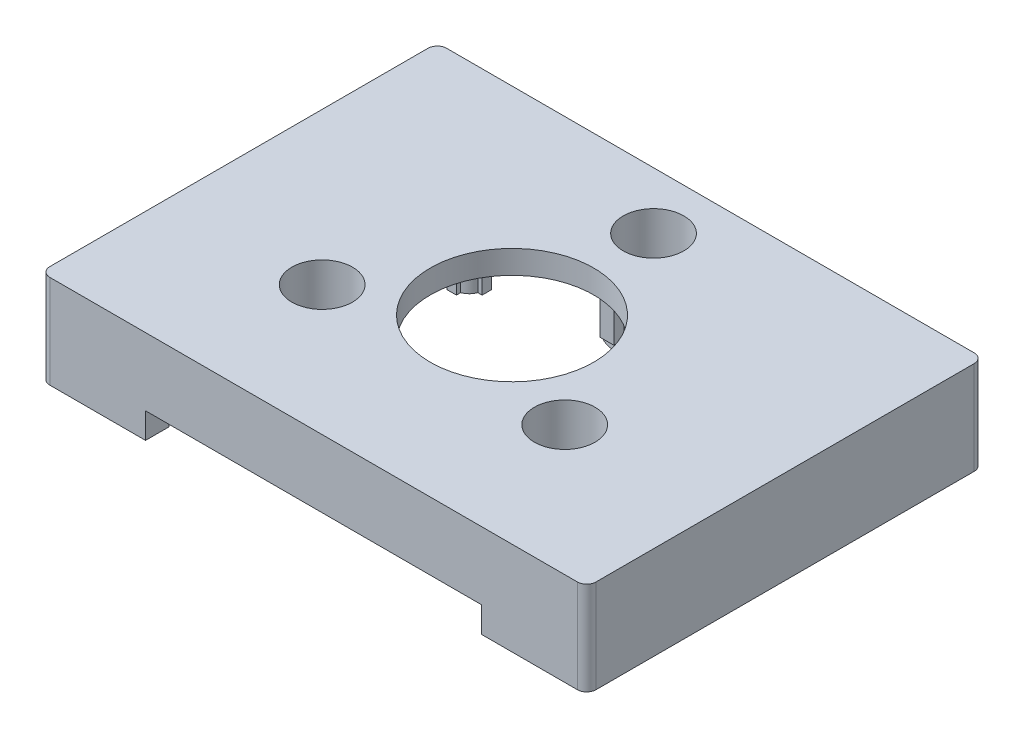
SolidWorks part; units mm, degrees
ref_plane "Front Plane" through (0, 0, 0) normal (0, 0, 1) x (1, 0, 0)
ref_plane "Top Plane" through (0, 0, 0) normal (0, 1, 0) x (1, 0, 0)
ref_plane "Right Plane" through (0, 0, 0) normal (1, 0, 0) x (0, 0, -1)
sketch "Sketch1" plane through (0, 0, 0) normal (0, 1, 0) x (1, 0, 0)
  line L1 (-58.5, 42.5) -> (58.5, 42.5)
  line L2 (-58.5, 42.5) -> (-58.5, -42.5)
  line L3 (-58.5, -42.5) -> (58.5, -42.5)
  line L4 (58.5, 42.5) -> (58.5, -42.5)
  dimension "D1" = 85
  dimension "D2" = 117
  dimension "D3" = 58.5
  dimension "D4" = 42.5
extrude "Boss-Extrude1" add sketch "Sketch1" along normal blind 20
sketch "Sketch2" plane through (0, 0, 0) normal (0, -1, 0) x (-1, 0, 0)
  line L0 (58.5, 42.5) -> (58.5, -42.5) construction
  line L1 (53.5, -37.5) -> (-53.5, -37.5)
  line L2 (53.5, -37.5) -> (53.5, 37.5)
  line L3 (53.5, 37.5) -> (-53.5, 37.5)
  line L4 (-53.5, -37.5) -> (-53.5, 37.5)
  line L5 (58.5, -42.5) -> (-58.5, -42.5) construction
  line L6 (-58.5, -42.5) -> (-58.5, 42.5) construction
  line L7 (-58.5, 42.5) -> (58.5, 42.5) construction
  dimension "D1" = 5
  dimension "D2" = 5
  dimension "D3" = 5
  dimension "D4" = 5
extrude "Cut-Extrude1" cut sketch "Sketch2" against normal blind 15
fillet "Fillet1" radius 2 1 edges at (-58.5, 10, 42.5)
fillet "Fillet2" radius 2 1 edges at (58.5, 10, 42.5)
fillet "Fillet3" radius 2 1 edges at (58.5, 10, -42.5)
fillet "Fillet4" radius 2 1 edges at (-58.5, 10, -42.5)
sketch "Sketch3" plane through (0, 0, 0) normal (0, -1, 0) x (1, 0, 0)
  line L0 (-56.5, 42.5) -> (56.5, 42.5) construction
  line L1 (-58.5, -40.5) -> (-58.5, 40.5) construction
  line L2 (58.5, 40.5) -> (58.5, -40.5) construction
  line L3 (56.5, -42.5) -> (-56.5, -42.5) construction
  circle A0 centre (-54.8, 38.8) radius 3.5
  circle A1 centre (54.8, 38.8) radius 3.5
  circle A2 centre (54.8, -38.8) radius 3.5
  circle A3 centre (-54.8, -38.8) radius 3.5
  dimension "D2" = 7
  dimension "D4" = 7
  dimension "D7" = 7
  dimension "D12" = 7
  dimension "D1" = 3.7
  dimension "D3" = 3.7
  dimension "D5" = 3.7
  dimension "D6" = 3.7
  dimension "D8" = 3.7
  dimension "D9" = 3.7
  dimension "D10" = 3.7
  dimension "D11" = 3.7
extrude "Boss-Extrude2" add sketch "Sketch3" against normal blind 16
sketch "Sketch4" plane through (0, 0, 0) normal (0, -1, 0) x (1, 0, 0)
  line L0 (56.5, -42.5) -> (-56.5, -42.5) construction
  line L1 (-58.5, -40.5) -> (-58.5, 40.5) construction
  line L2 (58.5, 40.5) -> (58.5, -40.5) construction
  line L3 (-56.5, 42.5) -> (56.5, 42.5) construction
  circle A0 centre (-54.8, 38.8) radius 1.5
  circle A1 centre (54.8, 38.8) radius 1.5
  circle A2 centre (54.8, -38.8) radius 1.5
  circle A3 centre (-54.8, -38.8) radius 1.5
  dimension "D1" = 3
  dimension "D4" = 3
  dimension "D5" = 3
  dimension "D8" = 3
  dimension "D2" = 3.7
  dimension "D3" = 3.7
  dimension "D6" = 3.7
  dimension "D7" = 3.7
  dimension "D9" = 3.7
  dimension "D10" = 3.7
extrude "Cut-Extrude2" cut sketch "Sketch4" against normal blind 15
sketch "Sketch5" plane through (0, 0, 42.5) normal (0, 0, 1) x (1, 0, 0)
  line L0 (-56.5, 0) -> (56.5, 0) construction
  line L1 (-36, 0) -> (36, 0)
  line L2 (-36, 0) -> (-36, 5.5)
  line L3 (-36, 5.5) -> (36, 5.5)
  line L4 (36, 0) -> (36, 5.5)
  line L5 (-56.5, 20) -> (-56.5, 0) construction
  dimension "D1" = 5.5
  dimension "D2" = 72
  dimension "D3" = 20.5
extrude "Cut-Extrude3" cut sketch "Sketch5" against normal blind 15
sketch "Sketch7" plane through (0, 15, -5.3154) normal (0, -1, 0) x (1, 0, 0)
  line L7 (27.4808, 10) -> (24.4808, 10)
  line L8 (27.4808, 10) -> (27.4808, 12.1419)
  line L9 (27.4808, 30) -> (24.4808, 30)
  line L10 (24.4808, 10) -> (24.4808, 12.1419)
  line L11 (35.9808, 18.5) -> (33.8389, 18.5)
  line L12 (35.9808, 18.5) -> (35.9808, 21.5)
  line L13 (35.9808, 21.5) -> (33.8389, 21.5)
  line L14 (15.9808, 18.5) -> (15.9808, 21.5)
  line L15 (-24.4808, 10) -> (-27.4808, 10)
  line L16 (-24.4808, 10) -> (-24.4808, 12.1419)
  line L17 (-24.4808, 30) -> (-27.4808, 30)
  line L18 (27.4808, 27.8581) -> (27.4808, 30)
  line L19 (24.4808, 27.8581) -> (24.4808, 30)
  line L20 (18.1226, 21.5) -> (15.9808, 21.5)
  line L21 (18.1226, 18.5) -> (15.9808, 18.5)
  line L22 (-27.4808, 10) -> (-27.4808, 12.1419)
  line L23 (-15.9808, 18.5) -> (-18.1226, 18.5)
  line L24 (1.5, -35) -> (-1.5, -35)
  line L25 (-15.9808, 18.5) -> (-15.9808, 21.5)
  line L26 (-15.9808, 21.5) -> (-18.1226, 21.5)
  line L27 (-35.9808, 18.5) -> (-35.9808, 21.5)
  line L28 (1.5, -35) -> (1.5, -32.8581)
  line L29 (1.5, -15) -> (-1.5, -15)
  line L31 (-24.4808, 27.8581) -> (-24.4808, 30)
  line L32 (-27.4808, 27.8581) -> (-27.4808, 30)
  line L33 (-33.8389, 21.5) -> (-35.9808, 21.5)
  line L34 (-33.8389, 18.5) -> (-35.9808, 18.5)
  line L35 (-1.5, -35) -> (-1.5, -32.8581)
  line L36 (10, -26.5) -> (7.8581, -26.5)
  line L37 (10, -26.5) -> (10, -23.5)
  line L38 (10, -23.5) -> (7.8581, -23.5)
  line L39 (-10, -26.5) -> (-10, -23.5)
  line L41 (-7.8581, -26.5) -> (-10, -26.5)
  line L42 (-7.8581, -23.5) -> (-10, -23.5)
  line L43 (-1.5, -17.1419) -> (-1.5, -15)
  line L44 (1.5, -17.1419) -> (1.5, -15)
  arc A1 (-7.8581, -26.5) -> (-1.5, -32.8581) centre (0, -25) ccw
  arc A3 (27.4808, 12.1419) -> (33.8389, 18.5) centre (25.9808, 20) ccw
  arc A4 (-18.1226, 21.5) -> (-24.4808, 27.8581) centre (-25.9808, 20) ccw
  arc A5 (1.5, -32.8581) -> (7.8581, -26.5) centre (0, -25) ccw
  arc A7 (33.8389, 21.5) -> (27.4808, 27.8581) centre (25.9808, 20) ccw
  arc A8 (18.1226, 18.5) -> (24.4808, 12.1419) centre (25.9808, 20) ccw
  arc A9 (24.4808, 27.8581) -> (18.1226, 21.5) centre (25.9808, 20) ccw
  arc A10 (-24.4808, 12.1419) -> (-18.1226, 18.5) centre (-25.9808, 20) ccw
  arc A11 (-33.8389, 18.5) -> (-27.4808, 12.1419) centre (-25.9808, 20) ccw
  arc A12 (-27.4808, 27.8581) -> (-33.8389, 21.5) centre (-25.9808, 20) ccw
  arc A13 (7.8581, -23.5) -> (1.5, -17.1419) centre (0, -25) ccw
  arc A14 (-1.5, -17.1419) -> (-7.8581, -23.5) centre (0, -25) ccw
  dimension "D2" = 16
  dimension "D3" = 16
  dimension "D4" = 16
  dimension "D8" = 51.9615
  dimension "D9" = 51.9615
  dimension "D10" = 51.9615
  dimension "D11" = 1.5
  dimension "D12" = 3
  dimension "D13" = 1.5
  dimension "D14" = 3
  dimension "D15" = 20
  dimension "D16" = 10
  dimension "D17" = 10
  dimension "D18" = 20
  dimension "D19" = 3
  dimension "D20" = 1.5
  dimension "D21" = 10
  dimension "D22" = 20
  dimension "D23" = 10
  dimension "D24" = 1.5
  dimension "D25" = 3
  dimension "D26" = 20
  dimension "D27" = 3
  dimension "D28" = 1.5
  dimension "D29" = 10
  dimension "D30" = 20
  dimension "D31" = 20
  dimension "D32" = 10
  dimension "D33" = 1.5
  dimension "D34" = 3
extrude "Boss-Extrude3" add sketch "Sketch7" along normal blind 10
sketch "Sketch8" plane through (0, 5, -5.3154) normal (0, -1, 0) x (1, 0, 0)
  circle A0 centre (-25.9808, 20) radius 6.5
  circle A1 centre (0, -25) radius 6.5
  circle A2 centre (25.9808, 20) radius 6.5
  dimension "D1" = 13
  dimension "D2" = 13
  dimension "D3" = 13
extrude "Cut-Extrude4" cut sketch "Sketch8" against normal through all
sketch "Sketch9" plane through (0, 5, -5.3154) normal (0, -1, 0) x (1, 0, 0)
  circle A0 centre (25.9808, 20) radius 8
  circle A1 centre (-25.9808, 20) radius 8
  circle A2 centre (0, -25) radius 8
  dimension "D1" = 16
  dimension "D2" = 16
  dimension "D3" = 16
extrude "Boss-Extrude4" add sketch "Sketch9" along normal blind 3
sketch "Sketch10" plane through (0, 2, -5.3154) normal (0, -1, 0) x (1, 0, 0)
  circle A0 centre (25.9808, 20) radius 1.75
  circle A1 centre (-25.9808, 20) radius 1.75
  circle A2 centre (0, -25) radius 1.75
  dimension "D1" = 3.5
  dimension "D2" = 3.5
  dimension "D3" = 3.5
extrude "Cut-Extrude5" cut sketch "Sketch10" against normal blind 3
sketch "Sketch12" plane through (0, 20, 0) normal (0, 1, 0) x (1, 0, 0)
  line L0 (-56.5, -42.5) -> (56.5, -42.5) construction
  circle A0 centre (0, 0) radius 17.5
  dimension "D1" = 35
  dimension "D2" = 42.5
extrude "Cut-Extrude6" cut sketch "Sketch12" against normal blind 5
sketch "Sketch13" plane through (0, 15, 0) normal (0, -1, 0) x (1, 0, 0)
  line L0 (0, 0) -> (0, 25)
  line L1 (0, 25) -> (0, -25)
  line L3 (20.6506, -8.75) -> (22.6506, -8.75)
  line L4 (20.6506, -8.75) -> (20.6506, -16.25)
  line L5 (20.6506, -16.25) -> (22.6506, -16.25)
  line L6 (22.6506, -8.75) -> (22.6506, -16.25)
  line L7 (17.9006, -11.5) -> (25.4006, -11.5)
  line L8 (17.9006, -11.5) -> (17.9006, -13.5)
  line L9 (17.9006, -13.5) -> (25.4006, -13.5)
  line L10 (25.4006, -11.5) -> (25.4006, -13.5)
  line L11 (-22.6506, -8.75) -> (-20.6506, -8.75)
  line L12 (-22.6506, -8.75) -> (-22.6506, -16.25)
  line L13 (-22.6506, -16.25) -> (-20.6506, -16.25)
  line L14 (-20.6506, -8.75) -> (-20.6506, -16.25)
  line L15 (-25.4006, -11.5) -> (-17.9006, -11.5)
  line L16 (-25.4006, -11.5) -> (-25.4006, -13.5)
  line L17 (-25.4006, -13.5) -> (-17.9006, -13.5)
  line L18 (-17.9006, -11.5) -> (-17.9006, -13.5)
  line L19 (-1, 28.75) -> (1, 28.75)
  line L20 (-1, 28.75) -> (-1, 21.25)
  line L21 (-1, 21.25) -> (1, 21.25)
  line L22 (1, 28.75) -> (1, 21.25)
  line L23 (-3.75, 26) -> (3.75, 26)
  line L24 (-3.75, 26) -> (-3.75, 24)
  line L25 (-3.75, 24) -> (3.75, 24)
  line L26 (3.75, 26) -> (3.75, 24)
  circle A0 centre (0, 0) radius 25
  circle A1 centre (0, 25) radius 3
  circle A2 centre (0, -25) radius 25
  circle A4 centre (21.6506, -12.5) radius 3
  circle A6 centre (-21.6506, -12.5) radius 3
  dimension "D1" = 6
  dimension "D2" = 6
  dimension "D3" = 6
  dimension "D4" = 50
  dimension "D5" = 1
  dimension "D6" = 2
  dimension "D7" = 7.5
  dimension "D8" = 3.75
  dimension "D9" = 1
  dimension "D10" = 2
  dimension "D11" = 7.5
  dimension "D12" = 3.75
  dimension "D13" = 2
  dimension "D14" = 2
  dimension "D15" = 1
  dimension "D16" = 1
  dimension "D17" = 7.5
  dimension "D18" = 3.75
  dimension "D19" = 3.75
  dimension "D20" = 7.5
  dimension "D21" = 7.5
  dimension "D22" = 2
  dimension "D23" = 1
  dimension "D24" = 2
  dimension "D25" = 1
  dimension "D26" = 3.75
  dimension "D27" = 3.75
  dimension "D28" = 7.5
extrude "Boss-Extrude6" add sketch "Sketch13" along normal blind 6 contours A1 L22 L19 L20 | L22 A1 L20 L23 | L23 A1 L22 | A0 A1 L23 L22 | A1 A0 L26 L23 | A1 L25 L26 A0 | L25 A1 A0 L22 | L22 A1 L25 | A1 L1 L21 L22 | A1 L20 L21 L1 | L20 A1 L0 L25 | L0 A1 L22 L25 | L22 A0 L0 L25 | L0 A0 L20 L25 | A0 L22 L23 L20 | L23 A1 A0 L20 | L20 A1 L23 | A1 L23 L24 A0 | A1 A0 L24 L25 | A0 A1 L25 L20 | L25 A1 L20 | A4 L6 L3 L4 | L6 A4 L4 A2 L7 A0 | L7 A2 L4 | A0 L7 L6 | A0 A4 L6 | L4 A4 A2 | A2 A4 L7 L4 | L7 A4 A0 L6 | L9 A4 L7 L6 | A4 L9 L10 L7 | A2 A4 L9 L6 | L6 A4 A2 | A2 L6 L9 | A2 L9 L6 L7 A0 | A2 A0 L7 | A0 A2 L7 L4 L9 | L9 A2 A0 | L4 A4 L6 A2 L9 A0 | L4 A0 L9 | L9 A4 A0 L4 | A0 A4 L4 | L7 A4 L9 L4 | A4 L7 L8 L9 | L14 A6 L12 A0 L15 A2 | A6 L14 L11 L12 | A6 L15 L16 L17 | L15 A6 L17 L12 | L17 A6 L15 L14 | A0 A6 L17 L14 | L12 A6 L14 A0 L17 A2 | L17 A6 A2 L12 | A2 A0 L15 L12 L17 | L15 A2 A0 L17 L14 | A0 A2 L17 | A2 L15 A0 | A0 L12 L15 | A0 A6 L15 L12 | L12 A6 A0 | A2 A6 L14 | L15 A6 A2 L14 | L14 A2 L15 | A2 L17 L12 | L17 A0 L14 | L14 A6 A0 | A2 A6 L12 | A6 L17 L18 L15 | A6 L12 L13 L14 | A4 L4 L5 L6
sketch "Sketch14" plane through (0, 9, 0) normal (0, -1, 0) x (1, 0, 0)
  circle A0 centre (21.6506, -12.5) radius 1.5
  dimension "D1" = 3
extrude "Cut-Extrude7" cut sketch "Sketch14" against normal blind 5
sketch "Sketch15" plane through (0, 9, 0) normal (0, -1, 0) x (1, 0, 0)
  circle A0 centre (-21.6506, -12.5) radius 1.5
  dimension "D1" = 3
extrude "Cut-Extrude8" cut sketch "Sketch15" against normal blind 5
sketch "Sketch16" plane through (0, 9, 0) normal (0, -1, 0) x (1, 0, 0)
  circle A0 centre (0, 25) radius 1.5
  dimension "D1" = 3
extrude "Cut-Extrude9" cut sketch "Sketch16" against normal blind 5
sketch "Sketch17" plane through (-53.5, 0, 0) normal (1, 0, 0) x (0, 0, -1)
  line L0 (-35.5504, 0) -> (35.5504, 0) construction
  line L1 (-30.5004, 0) -> (30.4996, 0)
  line L2 (-30.5004, 0) -> (-30.5004, 11.5)
  line L3 (-30.5004, 11.5) -> (30.4996, 11.5)
  line L4 (30.4996, 0) -> (30.4996, 11.5)
  line L5 (-35.5504, 15) -> (-35.5504, 0) construction
  line L6 (35.5504, 0) -> (35.5504, 15) construction
  line L7 (-35.5504, 15) -> (35.5504, 15) construction
  dimension "D1" = 61
  dimension "D2" = 5.05
  dimension "D3" = 5.0508
  dimension "D4" = 3.5
extrude "Cut-Extrude10" cut sketch "Sketch17" against normal blind 3.5
sketch "Sketch18" plane through (-57, 0, 0) normal (1, 0, 0) x (0, 0, -1)
  line L0 (30.4996, 11.5) -> (-30.5004, 11.5) construction
  line L1 (30.4996, 0) -> (30.4996, 11.5) construction
  line L2 (-30.5004, 11.5) -> (-30.5004, 0) construction
  line L3 (30.4996, 11.5) -> (-30.5004, 11.5) construction
  circle A0 centre (23.9996, 4) radius 1.5
  circle A1 centre (23.9996, 4) radius 3
  circle A2 centre (-14.0004, 8.95) radius 1.5
  circle A3 centre (-14.0004, 8.95) radius 3
  dimension "D3" = 3
  dimension "D4" = 6
  dimension "D7" = 3
  dimension "D8" = 6
  dimension "D1" = 7.5
  dimension "D2" = 6.5
  dimension "D5" = 16.5
  dimension "D6" = 2.55
extrude "Boss-Extrude7" add sketch "Sketch18" along normal blind 2
sketch "Sketch19" plane through (0, 0, 37.5) normal (0, 0, -1) x (-1, 0, 0)
  line L0 (-51.5504, 0) -> (-36, 0) construction
  line L1 (-36, 5.5) -> (-41, 5.5)
  line L2 (-36, 5.5) -> (-36, 0)
  line L3 (-36, 0) -> (-41, 0)
  line L4 (-41, 5.5) -> (-41, 0)
  dimension "D1" = 5
  dimension "D2" = 5.5
extrude "Cut-Extrude11" cut sketch "Sketch19" against normal blind 3
sketch "Sketch20" plane through (-53.5, 0, 0) normal (1, 0, 0) x (0, 0, -1)
  line L0 (30.4996, 11.5) -> (-30.5004, 11.5) construction
  line L1 (-30.5004, 11.5) -> (30.4996, 11.5)
  line L2 (-30.5004, 11.5) -> (-30.5004, 14)
  line L3 (-30.5004, 14) -> (30.4996, 14)
  line L4 (30.4996, 11.5) -> (30.4996, 14)
  line L5 (-30.5004, 11.5) -> (-30.5004, 0) construction
  dimension "D1" = 0
  dimension "D2" = 2.5
extrude "Cut-Extrude12" cut sketch "Sketch20" against normal blind 3.5
